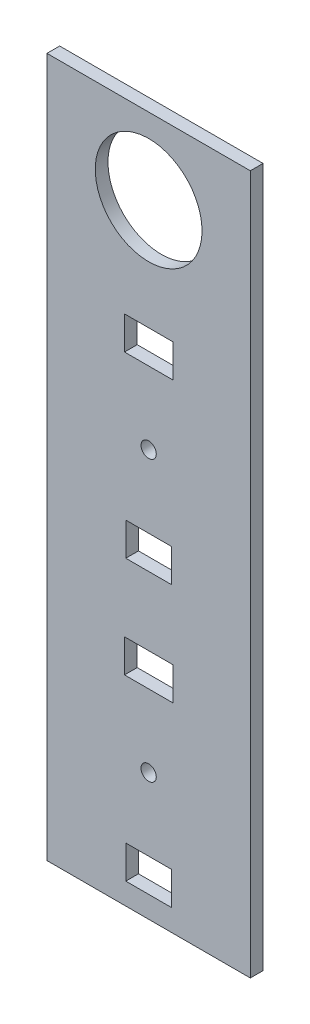
SolidWorks part; units mm, degrees
ref_plane "Plan de face" through (0, 0, 0) normal (0, 0, 1) x (1, 0, 0)
ref_plane "Plan de dessus" through (0, 0, 0) normal (0, 1, 0) x (1, 0, 0)
ref_plane "Plan de droite" through (0, 0, 0) normal (1, 0, 0) x (0, 0, -1)
sketch "Esquisse1" plane through (0, 0, 0) normal (0, 0, 1) x (1, 0, 0)
  line L1 (-40, 137.5) -> (40, 137.5)
  line L2 (-40, 137.5) -> (-40, -137.5)
  line L3 (-40, -137.5) -> (40, -137.5)
  line L4 (40, 137.5) -> (40, -137.5)
  dimension "D1" = 80
  dimension "D2" = 275
  dimension "D3" = 40
  dimension "D4" = 137.5
extrude "Boss.-Extru.1" add sketch "Esquisse1" against normal blind 5
sketch "Esquisse2" plane through (0, 0, 0) normal (0, 0, 1) x (1, 0, 0)
  line L0 (0, 137.5) -> (0, -137.5) construction
  line L1 (40, 137.5) -> (-40, 137.5) construction
  line L2 (-40, -137.5) -> (40, -137.5) construction
  line L3 (-40, 107.5) -> (40, 107.5) construction
  line L4 (-40, 137.5) -> (-40, -137.5) construction
  line L5 (40, -137.5) -> (40, 137.5) construction
  line L6 (-40, 72.5) -> (40, 72.5) construction
  line L7 (-40, 57.5) -> (40, 57.5) construction
  line L8 (-40, 22.5) -> (40, 22.5) construction
  line L9 (-40, -12.5) -> (40, -12.5) construction
  line L10 (-40, -37.5) -> (40, -37.5) construction
  line L11 (-40, -52.5) -> (40, -52.5) construction
  line L12 (-40, -87.5) -> (40, -87.5) construction
  line L13 (-40, -122.5) -> (40, -122.5) construction
  line L14 (-40, -132.5) -> (40, -132.5) construction
  line L15 (-40, -134.5) -> (40, -134.5) construction
  line L16 (-9, -116) -> (9, -116)
  line L17 (-9.5, 64) -> (9.5, 64)
  line L18 (-9.5, 64) -> (-9.5, 51)
  line L19 (-9.5, 51) -> (9.5, 51)
  line L20 (9.5, 64) -> (9.5, 51)
  line L21 (-9, -6) -> (9, -6)
  line L22 (-9, -6) -> (-9, -19)
  line L23 (-9, -19) -> (9, -19)
  line L24 (9, -6) -> (9, -19)
  line L25 (-9.5, -46) -> (9.5, -46)
  line L26 (-9.5, -46) -> (-9.5, -59)
  line L27 (-9.5, -59) -> (9.5, -59)
  line L28 (9.5, -46) -> (9.5, -59)
  line L29 (-9, -116) -> (-9, -129)
  line L30 (-9, -129) -> (9, -129)
  line L31 (9, -116) -> (9, -129)
  circle A0 centre (0, 107.5) radius 21
  circle A1 centre (0, 22.5) radius 3
  circle A2 centre (0, -87.5) radius 3
  dimension "D2" = 42
  dimension "D17" = 6
  dimension "D26" = 6
  dimension "D1" = 30
  dimension "D3" = 65
  dimension "D4" = 80
  dimension "D5" = 115
  dimension "D6" = 150
  dimension "D7" = 175
  dimension "D8" = 190
  dimension "D9" = 225
  dimension "D10" = 260
  dimension "D11" = 270
  dimension "D12" = 18
  dimension "D13" = 13
  dimension "D14" = 19
  dimension "D15" = 6.5
  dimension "D16" = 9.5
  dimension "D18" = 18
  dimension "D19" = 9
  dimension "D20" = 13
  dimension "D21" = 6.5
  dimension "D22" = 19
  dimension "D23" = 9.5
  dimension "D24" = 13
  dimension "D25" = 6.5
  dimension "D27" = 9
  dimension "D28" = 13
  dimension "D29" = 6.5
  dimension "D30" = 2
extrude "Enlèv. mat.-Extru.1" cut sketch "Esquisse2" against normal through all
